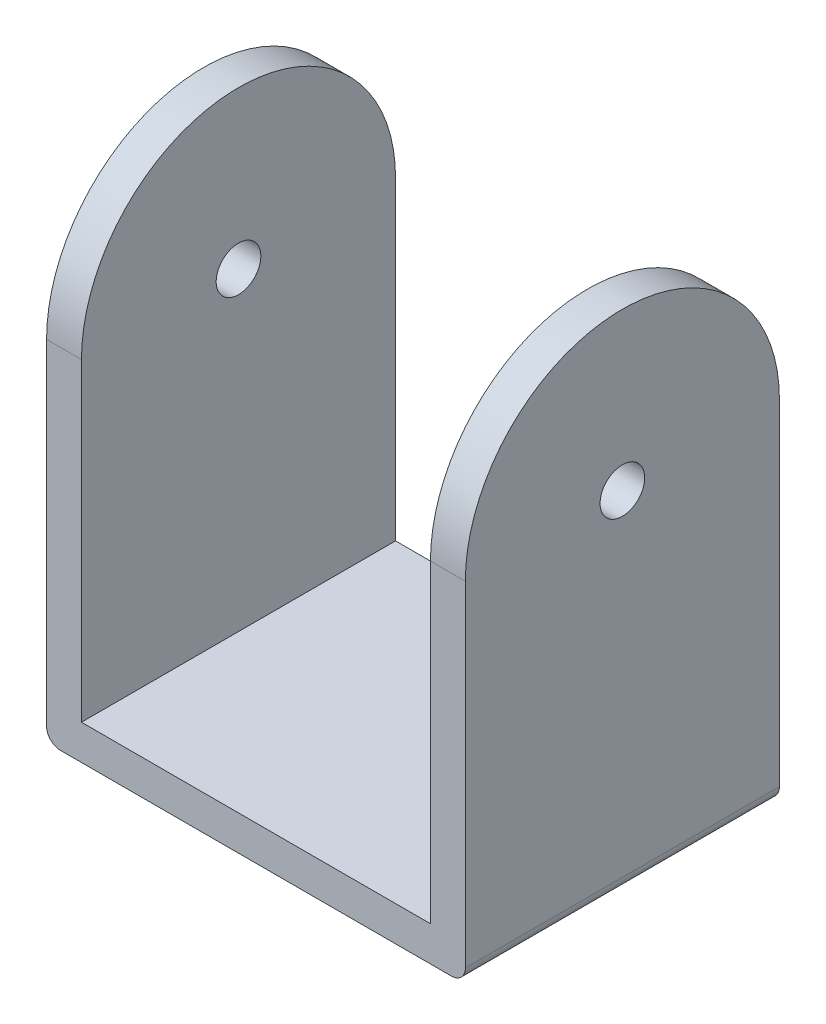
SolidWorks part; units mm, degrees
ref_plane "Front Plane" through (0, 0, 0) normal (0, 0, 1) x (1, 0, 0)
ref_plane "Top Plane" through (0, 0, 0) normal (0, 1, 0) x (1, 0, 0)
ref_plane "Right Plane" through (0, 0, 0) normal (1, 0, 0) x (0, 0, -1)
sketch "Sketch1" plane through (0, 0, 0) normal (1, 0, 0) x (0, 0, -1)
  line L1 (-11.25, -22.5) -> (11.25, -22.5)
  line L2 (-11.25, -22.5) -> (-11.25, 22.5)
  line L3 (-11.25, 22.5) -> (11.25, 22.5)
  line L4 (11.25, -22.5) -> (11.25, 22.5)
  line L5 (-11.25, -22.5) -> (11.25, 22.5) construction
  line L6 (-11.25, 22.5) -> (11.25, -22.5) construction
  arc A0 (-11.25, 0) -> (11.25, 0) centre (0, 0) cw
  point P0 (0, 0)
  dimension "D1" = 45
  dimension "D2" = 22.5
extrude "Boss-Extrude1" add sketch "Sketch1" along normal blind 2.5 contours A0 L2 L1 L4
ref_plane "Plane1" through (0, -22.5, 0) normal (0, -1, 0) x (-1, 0, 0)
sketch "Sketch2" plane through (0, -22.5, 0) normal (0, -1, 0) x (-1, 0, 0)
  line L1 (0, -11.25) -> (-27.5, -11.25)
  line L2 (0, -11.25) -> (0, 11.25)
  line L3 (0, 11.25) -> (-27.5, 11.25)
  line L4 (-27.5, -11.25) -> (-27.5, 11.25)
  dimension "D1" = 27.5
extrude "Boss-Extrude2" add sketch "Sketch2" along normal blind 2.5
ref_plane "Plane3" through (27.5, 0, 0) normal (1, 0, 0) x (0, 0, -1)
sketch "Sketch5" plane through (27.5, 0, 0) normal (1, 0, 0) x (0, 0, -1)
  line L1 (-11.25, -25) -> (11.25, -25)
  line L2 (-11.25, -25) -> (-11.25, 0)
  line L3 (-11.25, 0) -> (11.25, 0)
  line L4 (11.25, -25) -> (11.25, 0)
  arc A0 (-11.25, 0) -> (11.25, 0) centre (0, 0) cw
  dimension "D1" = 25
extrude "Boss-Extrude3" add sketch "Sketch5" along normal blind 2.5 contours A0 L3 | L1 L4 L3 L2
ref_plane "Plane4" through (30, 0, 0) normal (1, 0, 0) x (0, 0, -1)
sketch "Sketch6" plane through (30, 0, 0) normal (1, 0, 0) x (0, 0, -1)
  circle A0 centre (0, 0) radius 1.6
  dimension "D1" = 3.2
extrude "Cut-Extrude1" cut sketch "Sketch6" against normal blind 30
fillet "Fillet1" radius 1 2 edges at (0, -25, 0) (30, -25, 0)
